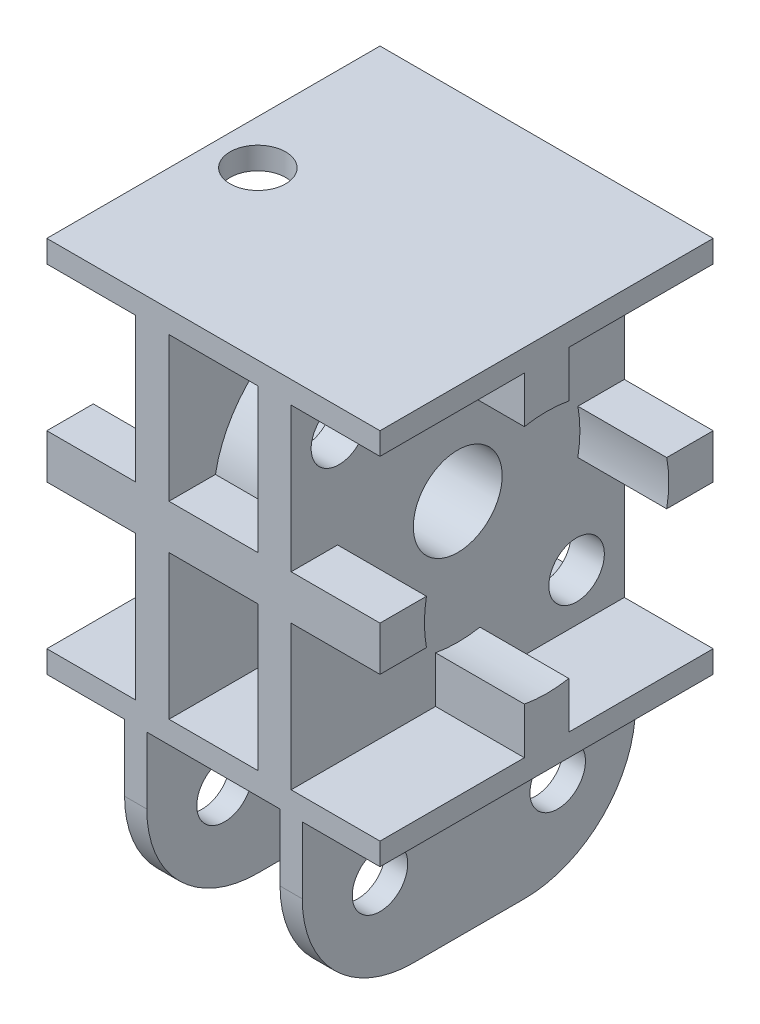
SolidWorks part; units mm, degrees
ref_plane "Alzado" through (0, 0, 0) normal (0, 0, 1) x (1, 0, 0)
ref_plane "Planta" through (0, 0, 0) normal (0, 1, 0) x (1, 0, 0)
ref_plane "Vista lateral" through (0, 0, 0) normal (1, 0, 0) x (0, 0, -1)
sketch "Croquis1" plane through (0, 0, 0) normal (0, 0, 1) x (1, 0, 0)
  line L0 (0, -16) -> (0, 16) construction
  line L1 (-15, -2) -> (-7, -2)
  line L2 (-15, -2) -> (-15, 2)
  line L3 (-15, 2) -> (-7, 2)
  line L4 (15, -2) -> (15, 2)
  line L5 (-15, -2) -> (15, 2) construction
  line L6 (-15, 2) -> (15, -2) construction
  line L7 (-4, 15) -> (4, 15)
  line L8 (-15, 17) -> (15, 17)
  line L9 (-15, 17) -> (-15, 15)
  line L10 (-15, 15) -> (-7, 15)
  line L11 (15, 17) -> (15, 15)
  line L12 (-15, 17) -> (15, 15) construction
  line L13 (-15, 15) -> (15, 17) construction
  line L14 (-15, -17) -> (-8, -17)
  line L15 (-15, -17) -> (-15, -15)
  line L16 (-15, -15) -> (-7, -15)
  line L17 (15, -17) -> (15, -15)
  line L18 (-15, -17) -> (15, -15) construction
  line L19 (-15, -15) -> (15, -17) construction
  line L21 (-7, 15) -> (-7, 2)
  line L23 (-4, 15) -> (-4, 2)
  line L25 (4, 15) -> (4, 2)
  line L27 (7, 15) -> (7, 2)
  line L29 (-7, -2) -> (-7, -15)
  line L31 (-4, -2) -> (-4, -15)
  line L33 (7, -2) -> (7, -15)
  line L35 (4, -2) -> (4, -15)
  line L36 (-4, 2) -> (4, 2)
  line L37 (-4, -2) -> (4, -2)
  line L38 (-4, -15) -> (4, -15)
  line L39 (7, -15) -> (15, -15)
  line L40 (7, -2) -> (15, -2)
  line L41 (7, 2) -> (15, 2)
  line L42 (7, 15) -> (15, 15)
  line L43 (-6, -17) -> (6, -17)
  line L45 (-8, -17) -> (-8, -33)
  line L46 (-8, -33) -> (-6, -33)
  line L47 (-6, -17) -> (-6, -33)
  line L49 (8, -17) -> (8, -33)
  line L50 (8, -33) -> (6, -33)
  line L51 (6, -17) -> (6, -33)
  line L52 (8, -17) -> (15, -17)
  point P0 (0, 0)
  point P9 (0, 0)
  dimension "D1" = 30
  dimension "D2" = 4
  dimension "D3" = 32
  dimension "D4" = 2
  dimension "D5" = 30
  dimension "D6" = 2
  dimension "D7" = 6
  dimension "D8" = 4
  dimension "D9" = 6
  dimension "D10" = 30
  dimension "D11" = 4
  dimension "D12" = 3
  dimension "D13" = 3
  dimension "D16" = 2
  dimension "D17" = 2
  dimension "D18" = 16
  dimension "D19" = 16
extrude "Saliente-Extruir1" add sketch "Croquis1" along normal mid plane 30
sketch "Croquis3" plane through (0, 0, 0) normal (1, 0, 0) x (0, 0, -1)
  circle A0 centre (0, 0) radius 11
  dimension "D1" = 22
extrude "Cortar-Extruir1" cut sketch "Croquis3" against normal mid plane 30
sketch "Croquis4" plane through (8, 0, 0) normal (1, 0, 0) x (0, 0, -1)
  line L0 (0, -17) -> (0, -33) construction
  line L1 (-15, -17) -> (15, -17) construction
  line L2 (-15, -33) -> (15, -33) construction
  line L3 (-15, -25) -> (15, -25) construction
  line L4 (15, -33) -> (15, -17) construction
  circle A0 centre (-8, -25) radius 2.5
  circle A1 centre (8, -25) radius 2.5
  point P11 (0, -25)
  dimension "D1" = 5
  dimension "D2" = 5
  dimension "D3" = 8
  dimension "D4" = 8
extrude "Cortar-Extruir2" cut sketch "Croquis4" against normal blind 30
fillet "Redondeo1" radius 10 4 edges at (-7, -33, 15) (7, -33, 15) (-7, -33, -15) (7, -33, -15)
sketch "Croquis5" plane through (0, 17, 0) normal (0, 1, 0) x (1, 0, 0)
  line L0 (-11, 0) -> (11, 0) construction
  circle A0 centre (-11, 0) radius 2.5
  circle A1 centre (11, 0) radius 2.5
  point P4 (0, 0)
  dimension "D2" = 5
  dimension "D3" = 5
  dimension "D1" = 22
extrude "Cortar-Extruir3" cut sketch "Croquis5" against normal blind 2
sketch "Sketch1" plane through (7, 0, 0) normal (1, 0, 0) x (0, 0, -1)
  line L0 (-2, 15) -> (2, 15)
  line L1 (2, 15) -> (2, 10.8167)
  line L2 (-2, 15) -> (-2, 10.8167)
  line L5 (-15, 15) -> (15, 15) construction
  arc A0 (10.8167, 2) -> (-10.8167, 2) centre (0, 0) ccw construction
  arc A1 (2, 10.8167) -> (-2, 10.8167) centre (0, 0) ccw
  point P9 (0, 15)
  dimension "D1" = 4
extrude "Boss-Extrude1" add sketch "Sketch1" along normal up to surface (8 mm away) up to face at (15, 0, 12.9542)
mirror "Mirror1" about plane through (0, 0, 0) normal (0, 1, 0) of "Boss-Extrude1"
sketch "Sketch2" plane through (7, 0, 0) normal (1, 0, 0) x (0, 0, -1)
  line L0 (-10.7, 10.7) -> (-10.7, 15) construction
  line L1 (-15, 15) -> (-2, 15) construction
  line L2 (-10.7, 10.7) -> (-15, 10.7) construction
  line L3 (-15, 2) -> (-15, 15) construction
  line L4 (10.7, -10.7) -> (15, -10.7) construction
  line L5 (15, -15) -> (15, -2) construction
  line L6 (10.7, -10.7) -> (10.7, -15) construction
  line L8 (2, -15) -> (15, -15) construction
  circle A0 centre (-10.7, 10.7) radius 2.5
  circle A1 centre (10.7, -10.7) radius 2.5
  dimension "D1" = 5
  dimension "D2" = 5
  dimension "D3" = 4.3
  dimension "D4" = 4.3
extrude "Cut-Extrude1" cut sketch "Sketch2" against normal up to surface (3 mm away) up to face at (4, 7.8333, 0)
sketch "Sketch3" plane through (-7, 0, 0) normal (-1, 0, 0) x (0, 0, 1)
  circle A0 centre (0, 0) radius 11
  circle A1 centre (0, 0) radius 4
  dimension "D1" = 8
extrude "Boss-Extrude2" add sketch "Sketch3" against normal up to surface (11 mm away)
mirror "Mirror2" about plane through (0, 0, 0) normal (1, 0, 0) of "Boss-Extrude2"
sketch "Sketch4" plane through (0, 17, 0) normal (0, 1, 0) x (1, 0, 0)
  circle A1 centre (11, 0) radius 2.5
  circle A2 centre (11, 0) radius 2.5 construction
extrude "Boss-Extrude4" add sketch "Sketch4" against normal up to surface (2 mm away) up to face at (11, 15, -6.4167)
